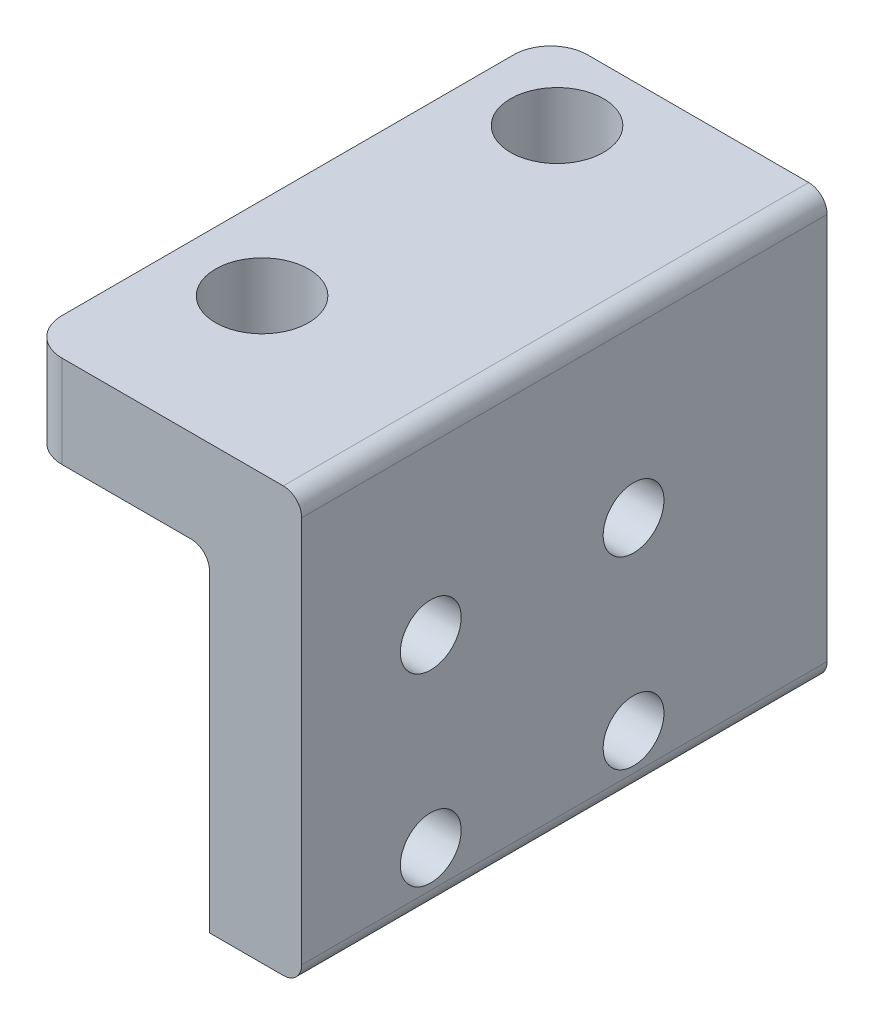
SolidWorks part; units mm, degrees
material "6063-T5"
ref_plane "前视基准面" through (0, 0, 0) normal (0, 0, 1) x (1, 0, 0)
ref_plane "上视基准面" through (0, 0, 0) normal (0, 1, 0) x (1, 0, 0)
ref_plane "右视基准面" through (0, 0, 0) normal (1, 0, 0) x (0, 0, -1)
other "Configuration Table"
sketch "草图1" plane through (0, 0, 0) normal (0, 0, 1) x (1, 0, 0)
  line L0 (0, 0) -> (-10, 0)
  line L1 (-10, 0) -> (-10, 5)
  line L2 (-10, 5) -> (5, 5)
  line L3 (5, 5) -> (5, -18)
  line L4 (5, -18) -> (0, -18)
  line L5 (0, -18) -> (0, 0)
  dimension "D1" = 5
  dimension "D2" = 15
  dimension "D3" = 23
extrude "凸台-拉伸1" add sketch "草图1" along normal blind 28.5
sketch "草图2" plane through (0, 5, 0) normal (0, 1, 0) x (1, 0, 0)
  line L0 (-10, -14.25) -> (5, -14.25) construction
  line L1 (-10, -28.5) -> (-10, 0) construction
  line L2 (5, -28.5) -> (5, 0) construction
  line L3 (5, -28.5) -> (-10, -28.5) construction
  circle A0 centre (-5.5, -4.15) radius 2.525
  circle A1 centre (-5.5, -20.15) radius 2.525
  point P12 (0, 0)
  dimension "D1" = 5.05
  dimension "D3" = 16
  dimension "D2" = 8.35
  dimension "D4" = 4.5
extrude "切除-拉伸1" cut sketch "草图2" against normal blind 28.5
sketch "草图3" plane through (0, 0, 0) normal (-1, 0, 0) x (0, 0, 1)
  line L1 (10.5, -15) -> (21.5, -15) construction
  line L2 (10.5, -15) -> (10.5, -5) construction
  line L3 (10.5, -5) -> (21.5, -5) construction
  line L4 (21.5, -15) -> (21.5, -5) construction
  line L5 (10.5, -15) -> (21.5, -5) construction
  line L6 (10.5, -5) -> (21.5, -15) construction
  line L7 (28.5, 0) -> (28.5, -18) construction
  line L8 (28.5, -18) -> (0, -18) construction
  circle A0 centre (10.5, -5) radius 1.525
  circle A1 centre (10.5, -15) radius 1.525
  circle A2 centre (21.5, -15) radius 1.525
  circle A3 centre (21.5, -5) radius 1.525
  point P0 (16, -10)
  dimension "D2" = 3.05
  dimension "D5" = 3
  dimension "D1" = 11
  dimension "D3" = 7
  dimension "D4" = 10
hole_wizard "M4 螺纹孔1" positions "3D草图1" profile "草图4" tap size "M4" standard "GB" end condition through all
sketch3d "3D草图1"
  point P0 (0, -5, 10.5)
  point P3 (0, -15, 10.5)
  point P6 (0, -15, 21.5)
  point P9 (0, -5, 21.5)
sketch "草图4" plane through (0, -5, 10.5) normal (0, 1, 0) x (0, 0, 1)
  line L0 (0, 0) -> (0, 5)
  line L1 (0, 5) -> (1.65, 5)
  line L2 (1.65, 5) -> (1.65, 0)
  line L5 (1.65, 0) -> (0, 0)
  line L11 (0, -6.35) -> (0, 107.95) construction
  dimension "通孔螺纹孔钻头直径" = 3.3
  dimension "通孔螺纹孔钻头深度" = 5
cosmetic thread "孔螺蚊线1" parameters "D2"=4
cosmetic thread "孔螺蚊线2" parameters "D2"=4
cosmetic thread "孔螺蚊线3" parameters "D2"=4
cosmetic thread "孔螺蚊线4" parameters "D2"=4
fillet "圆角1" radius 2 2 edges at (-10, 2.5, 0) (-10, 2.5, 28.5)
fillet "圆角2" radius 1 3 edges at (5, -18, 14.25) (0, 0, 14.25) (5, 5, 14.25)
